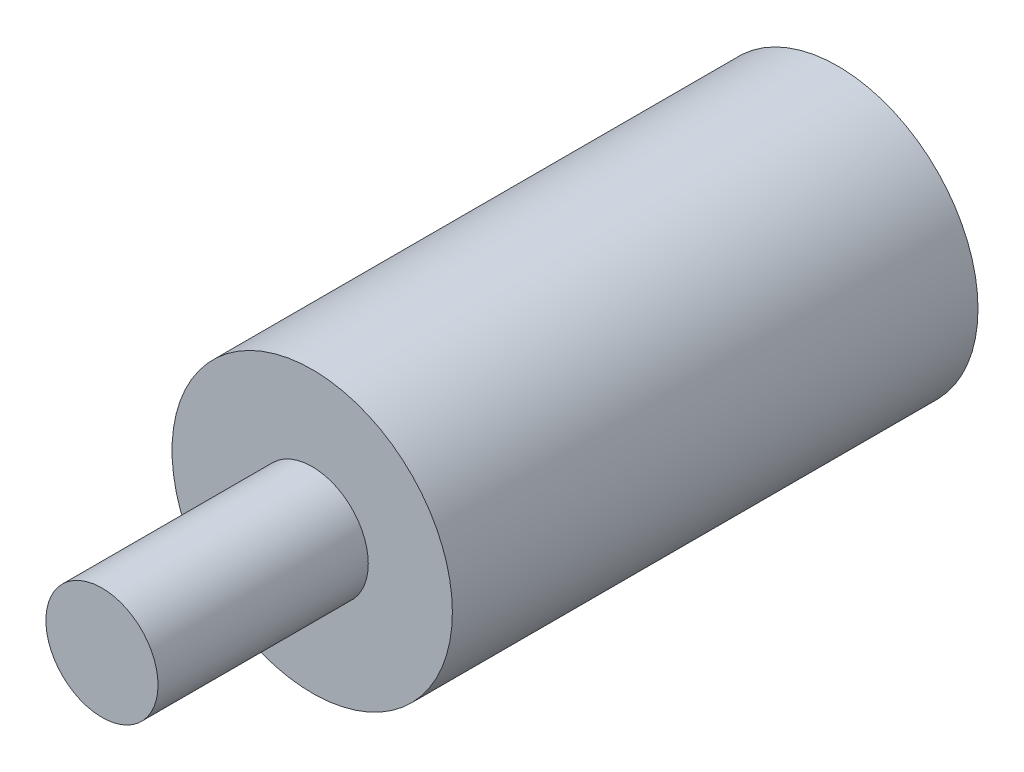
SolidWorks part; units mm, degrees
ref_plane "Front" through (0, 0, 0) normal (0, 0, 1) x (1, 0, 0)
ref_plane "Top" through (0, 0, 0) normal (0, 1, 0) x (1, 0, 0)
ref_plane "Right" through (0, 0, 0) normal (1, 0, 0) x (0, 0, -1)
sketch "Эскиз2" plane through (0, 0, 0) normal (0, 0, 1) x (1, 0, 0)
  circle A0 centre (0, 0) radius 100
extrude "Бобышка-Вытянуть1" add sketch "Эскиз2" along normal blind 375
sketch "Эскиз3" plane through (0, 0, 375) normal (0, 0, 1) x (1, 0, 0)
  circle A0 centre (0, 0) radius 40
extrude "Бобышка-Вытянуть2" add sketch "Эскиз3" along normal blind 150
